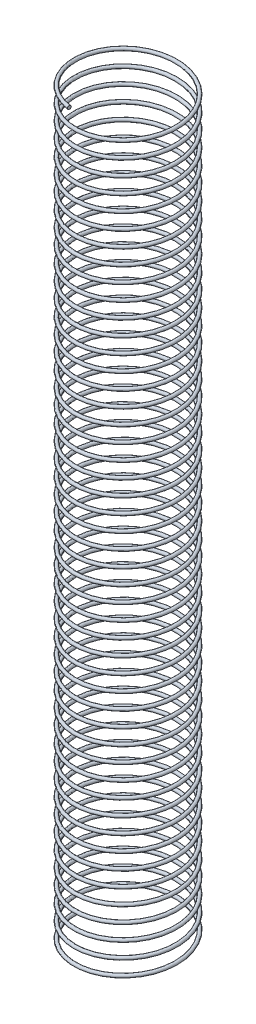
SolidWorks part; units mm, degrees
ref_plane "Front Plane" through (0, 0, 0) normal (0, 0, 1) x (1, 0, 0)
ref_plane "Top Plane" through (0, 0, 0) normal (0, 1, 0) x (1, 0, 0)
ref_plane "Right Plane" through (0, 0, 0) normal (1, 0, 0) x (0, 0, -1)
sketch "Sketch1" plane through (0, 0, 0) normal (0, 1, 0) x (1, 0, 0)
  circle A0 centre (0, 0) radius 150
  dimension "D1" = 300
curve "Helix/Spiral1" pitch 45 height 2170 turns 48.2222
sketch "Sketch3" plane through (0, 0, 0) normal (0, 0, 1) x (1, 0, 0)
  circle A0 centre (-148.1506, 0) radius 5
sweep "Sweep1" add profiles "Sketch3" path "Helix/Spiral1"
sketch "Sketch4" plane through (0, 0, 0) normal (0, 0, 1) x (1, 0, 0)
  line L0 (0, 0) -> (0, 2081.1012) construction
